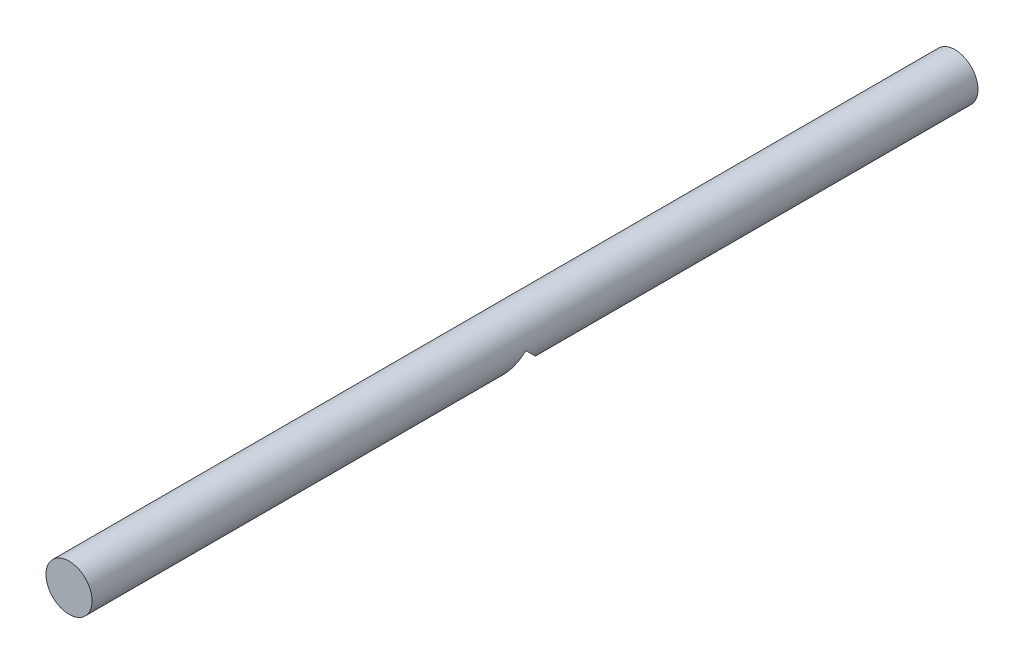
SolidWorks part; units mm, degrees
ref_plane "Front Plane" through (0, 0, 0) normal (0, 0, 1) x (1, 0, 0)
ref_plane "Top Plane" through (0, 0, 0) normal (0, 1, 0) x (1, 0, 0)
ref_plane "Right Plane" through (0, 0, 0) normal (1, 0, 0) x (0, 0, -1)
sketch "Sketch1" plane through (0, 0, 0) normal (0, 0, 1) x (1, 0, 0)
  circle A0 centre (0, 0) radius 12.5
  dimension "D1" = 25
extrude "Boss-Extrude1" add sketch "Sketch1" along normal blind 480
sketch "Sketch2" plane through (0, 0, 0) normal (0, 1, 0) x (1, 0, 0)
  line L0 (0, 0) -> (0, -245) construction
  circle A0 centre (0, -245) radius 12.5
  dimension "D2" = 25
  dimension "D1" = 245
extrude "Cut-Extrude3" cut sketch "Sketch2" against normal blind 20
